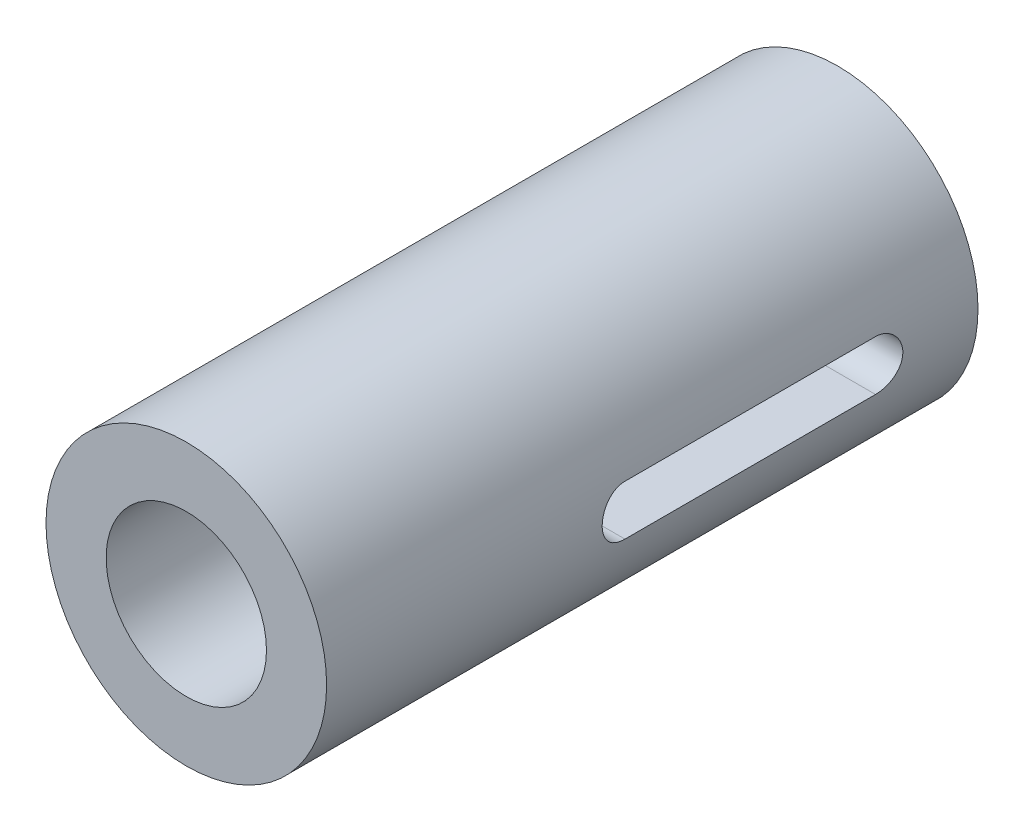
SolidWorks part; units mm, degrees
ref_plane "Piano frontale" through (0, 0, 0) normal (0, 0, 1) x (1, 0, 0)
ref_plane "Piano superiore" through (0, 0, 0) normal (0, 1, 0) x (1, 0, 0)
ref_plane "Piano destro" through (0, 0, 0) normal (1, 0, 0) x (0, 0, -1)
sketch "Schizzo1" plane through (0, 0, 0) normal (0, 0, 1) x (1, 0, 0)
  circle A0 centre (0, 0) radius 14
  circle A1 centre (0, 0) radius 8
  dimension "D1" = 16
  dimension "D2" = 28
extrude "Estrusione-Estrusione1" add sketch "Schizzo1" along normal blind 20
sketch "Schizzo2" plane through (0, 0, 0) normal (1, 0, 0) x (0, 0, -1)
  line L0 (0, 0) -> (61.4588, 0) construction
  line L1 (0, -14) -> (45, -14)
  line L2 (0, -14) -> (0, 14)
  line L3 (0, 14) -> (45, 14)
  line L4 (45, -14) -> (45, 14)
  line L5 (35, -2.5) -> (10, -2.5)
  line L7 (35, 2.5) -> (10, 2.5)
  line L11 (0, -14) -> (0, 14) construction
  line L12 (0, -14) -> (0, 14) construction
  arc A0 (35, -2.5) -> (35, 2.5) centre (35, 0) ccw
  arc A1 (10, -2.5) -> (10, 2.5) centre (10, 0) cw
  point P13 (22.5, -2.5)
  point P14 (22.5, -14)
  dimension "D1" = 5
  dimension "D3" = 45
  dimension "D4" = 25
extrude "Estrusione-Estrusione2" add sketch "Schizzo2" along normal up to surface and the other way up to surface up to face at (14, 0, 20) other way up to face at (14, 0, 20)
